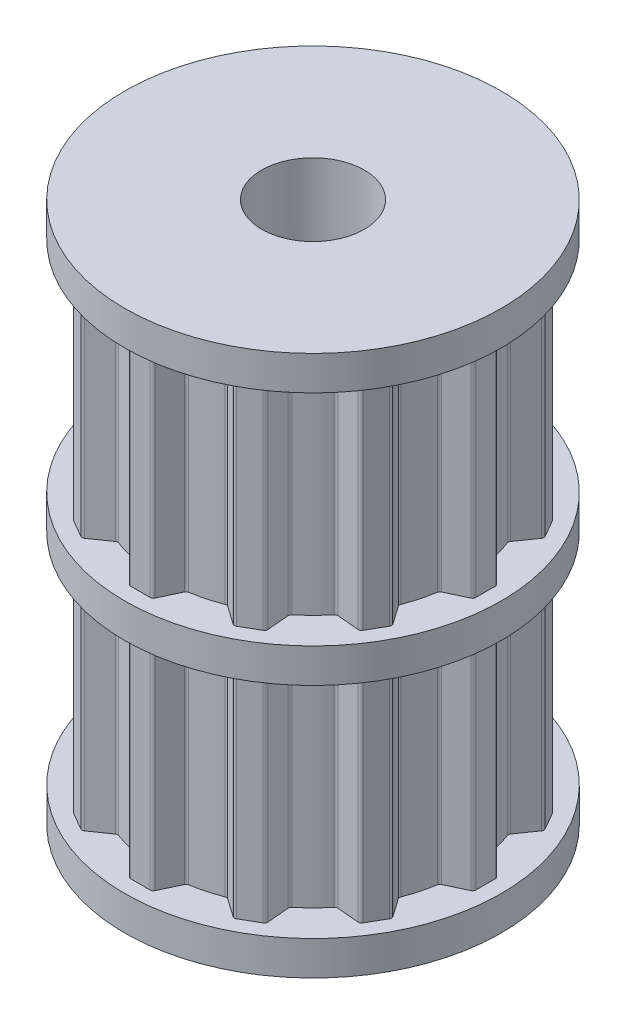
SolidWorks part; units mm, degrees
ref_plane "Front Plane" through (0, 0, 0) normal (0, 0, 1) x (1, 0, 0)
ref_plane "Top Plane" through (0, 0, 0) normal (0, 1, 0) x (1, 0, 0)
ref_plane "Right Plane" through (0, 0, 0) normal (1, 0, 0) x (0, 0, -1)
sketch "草圖1" plane through (0, 0, 0) normal (0, 1, 0) x (1, 0, 0)
  circle A0 centre (0, 0) radius 8.81
  dimension "D1" = 17.62
extrude "填料-伸長1" add sketch "草圖1" along normal mid plane 27.6
sketch "草圖7" plane through (0, -13.8, 0) normal (0, -1, 0) x (1, 0, 0)
  line L0 (0, -8.81) -> (0, 0) construction
  line L1 (-1.7513, -7.81) -> (1.7513, -7.81)
  line L2 (-1.7513, -7.81) -> (-0.6928, -10.08)
  line L3 (-0.6928, -10.08) -> (0.6928, -10.08)
  line L4 (0.6928, -10.08) -> (1.7513, -7.81)
  line L5 (-1.285, -8.81) -> (1.285, -8.81) construction
  circle A0 centre (0, 0) radius 8.81 construction
  point P8 (0, -7.81)
  point P13 (0, -8.81)
  dimension "D1" = 1.27
  dimension "D2" = 1
  dimension "D3" = 2.57
  dimension "50" = 50
extrude "填料-伸長5" add sketch "草圖7" against normal through all
fillet "圓角1" radius 0.19 4 edges at (0.6928, 0, -10.08) (-0.6928, 0, -10.08) (-1.3322, 0, -8.7087) (1.3322, 0, -8.7087)
pattern_circular "環狀複製排列1" count 12 over 360 about axis through (0, 0, 0) along (0, 1, 0) of "圓角1", "填料-伸長5"
sketch "草圖3" plane through (0, -13.8, 0) normal (0, -1, 0) x (1, 0, 0)
  circle A0 centre (0, 0) radius 11
  dimension "D1" = 22
extrude "填料-伸長3" add sketch "草圖3" along normal blind 2
sketch "草圖4" plane through (0, 13.8, 0) normal (0, 1, 0) x (1, 0, 0)
  circle A0 centre (0, 0) radius 11
  dimension "D1" = 22
extrude "填料-伸長4" add sketch "草圖4" along normal blind 2
sketch "草圖5" plane through (0, -15.8, 0) normal (0, -1, 0) x (1, 0, 0)
  circle A0 centre (0, 0) radius 3
  dimension "D1" = 6
extrude "除料-伸長1" cut sketch "草圖5" against normal through all
sketch "草圖8" plane through (0, 15.8, 0) normal (0, 1, 0) x (1, 0, 0)
  circle A0 centre (0, 0) radius 11
  dimension "D1" = 22
extrude "填料-伸長6" add sketch "草圖8" along normal mid plane 2 from offset 15.8
